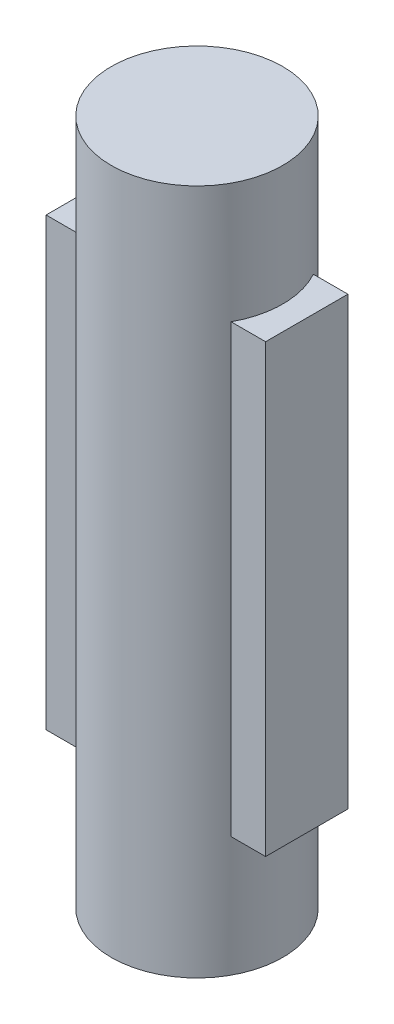
SolidWorks part; units mm, degrees
ref_plane "Front Plane" through (0, 0, 0) normal (0, 0, 1) x (1, 0, 0)
ref_plane "Top Plane" through (0, 0, 0) normal (0, 1, 0) x (1, 0, 0)
ref_plane "Right Plane" through (0, 0, 0) normal (1, 0, 0) x (0, 0, -1)
sketch "Sketch1" plane through (0, 0, 0) normal (0, 1, 0) x (1, 0, 0)
  circle A0 centre (0, 0) radius 3.175
  dimension "D1" = 6.35
extrude "Boss-Extrude1" add sketch "Sketch1" along normal mid plane 25.4
sketch "Sketch2" plane through (0, 0, 0) normal (0, 1, 0) x (1, 0, 0)
  line L1 (-4.064, -1.524) -> (4.064, -1.524)
  line L2 (-4.064, -1.524) -> (-4.064, 1.524)
  line L3 (-4.064, 1.524) -> (4.064, 1.524)
  line L4 (4.064, -1.524) -> (4.064, 1.524)
  line L5 (-4.064, -1.524) -> (4.064, 1.524) construction
  line L6 (-4.064, 1.524) -> (4.064, -1.524) construction
  point P0 (0, 0)
  dimension "D1" = 3.048
  dimension "D2" = 8.128
extrude "Boss-Extrude2" add sketch "Sketch2" along normal mid plane 16.51
